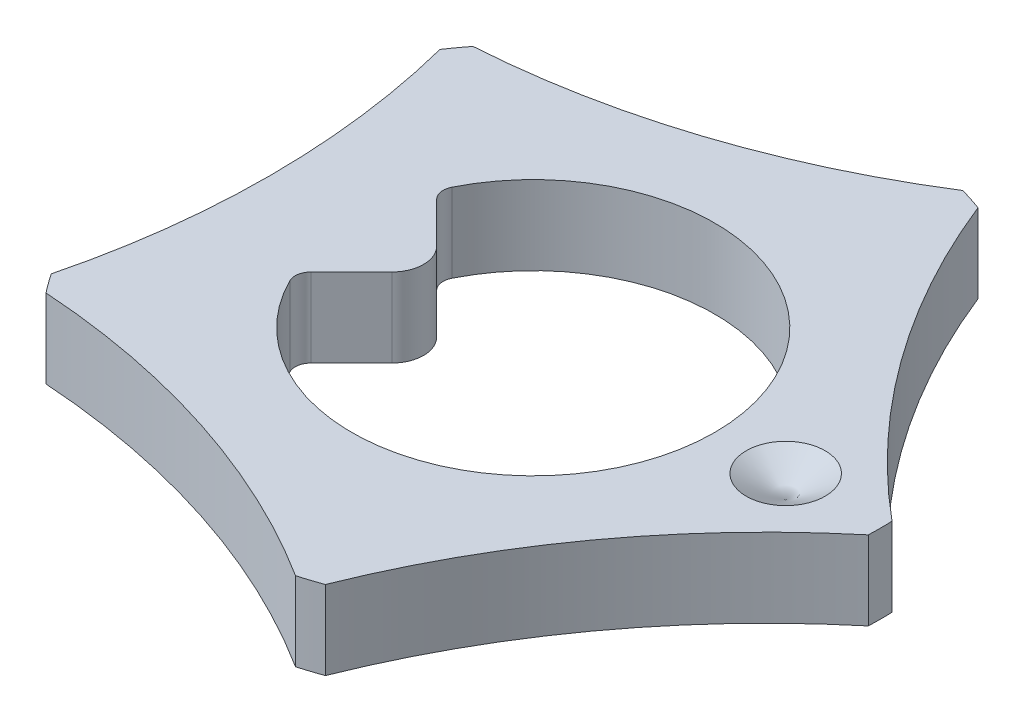
SolidWorks part; units mm, degrees
ref_plane "Front Plane" through (0, 0, 0) normal (0, 0, 1) x (1, 0, 0)
ref_plane "Top Plane" through (0, 0, 0) normal (0, 1, 0) x (1, 0, 0)
ref_plane "Right Plane" through (0, 0, 0) normal (1, 0, 0) x (0, 0, -1)
sketch "Sketch2" plane through (0, 0, 0) normal (0, 1, 0) x (1, 0, 0)
  circle A0 centre (0, 0) radius 2.2
  dimension "D1" = 4.4
extrude "Boss-Extrude2" add sketch "Sketch2" along normal blind 0.5 contours A0
sketch "Sketch3" plane through (0, 0.5, 0) normal (0, 1, 0) x (1, 0, 0)
  line L0 (0, 0) -> (2.2, 0) construction
  line L1 (0, 0) -> (0.6798, -2.0923) construction
  line L2 (0, 0) -> (-0.6798, -2.0923) construction
  line L3 (0, 0) -> (0, -2.2) construction
  circle A0 centre (0, 0) radius 2.2 construction
  arc A1 (0.7508, 2.0679) -> (2.1987, 0.075) centre (5.3952, 3.9198) ccw
  arc A2 (2.1987, -0.075) -> (0.7508, -2.0679) centre (5.3952, -3.9198) ccw
  arc A3 (0.6081, -2.1143) -> (-1.7347, -1.353) centre (-2.0608, -6.3424) ccw
  arc A4 (-1.7347, 1.353) -> (-1.8229, 1.2317) centre (0, 0) ccw
  arc A5 (-1.8229, -1.2317) -> (-1.8229, 1.2317) centre (-6.6688, 0) ccw
  arc A6 (-1.7347, 1.353) -> (0.6081, 2.1143) centre (-2.0608, 6.3424) ccw
  arc A7 (-1.8229, -1.2317) -> (-1.7347, -1.353) centre (0, 0) ccw
  arc A8 (0.7508, 2.0679) -> (0.6081, 2.1143) centre (0, 0) ccw
  arc A9 (2.1987, -0.075) -> (2.1987, 0.075) centre (0, 0) ccw
  arc A10 (0.6081, -2.1143) -> (0.7508, -2.0679) centre (0, 0) ccw
  point P25 (0, 0)
  dimension "D3" = 5
  dimension "D4" = 5
  dimension "D1" = 72
  dimension "D2" = 72
  dimension "D5" = 0.15
extrude "Cut-Extrude1" cut sketch "Sketch3" against normal blind 0.5 flip side to cut
other "Flex4" [suppressed] parameters "D0"=2, "D1"=0, "D2"=0
sketch "Sketch4" plane through (0, 0.5, 0) normal (0, 1, 0) x (1, 0, 0)
  line L0 (0, 0) -> (-1.15, 0) construction
  line L1 (-1.0594, 0.4474) -> (-0.612, 0)
  line L2 (-0.612, 0) -> (-1.0594, -0.4474)
  arc A0 (-1.0594, -0.4474) -> (-1.0594, 0.4474) centre (0, 0) ccw
  dimension "D1" = 2.3
  dimension "D2" = 0.612
extrude "Cut-Extrude2" cut sketch "Sketch4" against normal up to next
fillet "Fillet1" radius 0.2 1 edges at (-0.612, 0.25, 0)
fillet "Fillet2" radius 0.1 2 edges at (-1.0594, 0.25, 0.4474) (-1.0594, 0.25, -0.4474)
sketch "Sketch6" plane through (0, 0, 0) normal (0, 0, 1) x (1, 0, 0)
  line L0 (1.6, 0.5) -> (1.6, 0.1807) construction
  line L1 (2.1987, 0.5) -> (0.7508, 0.5) construction
  line L2 (1.6, 0.5) -> (1.6, 0.3557)
  line L3 (1.6, 0.3557) -> (1.85, 0.5)
  line L4 (1.6, 0.5) -> (1.85, 0.5)
  dimension "D1" = 1.6
  dimension "D2" = 60
  dimension "D3" = 0.5
revolve "Cut-Revolve7" cut sketch "Sketch6" angle 360 about L0
